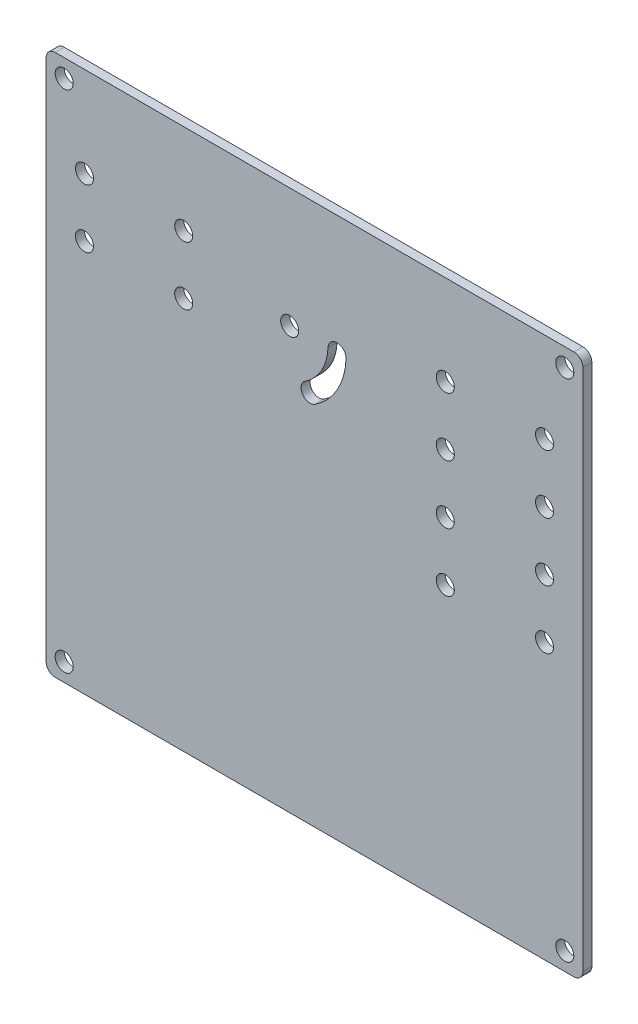
SolidWorks part; units mm, degrees
ref_plane "前视基准面" through (0, 0, 0) normal (0, 0, 1) x (1, 0, 0)
ref_plane "上视基准面" through (0, 0, 0) normal (0, 1, 0) x (1, 0, 0)
ref_plane "右视基准面" through (0, 0, 0) normal (1, 0, 0) x (0, 0, -1)
other "Configuration Table"
sketch "草图2" plane through (0, 0, 0) normal (0, 0, 1) x (1, 0, 0)
  line L1 (0, 0) -> (119, 0)
  line L2 (0, 0) -> (0, 120)
  line L3 (0, 120) -> (119, 120)
  line L4 (119, 0) -> (119, 120)
  dimension "D1" = 119
  dimension "D2" = 120
extrude "凸台-拉伸1" add sketch "草图2" along normal blind 2 contours L3 L4 L1 L2
sketch "草图4" plane through (0, 0, 2) normal (0, 0, 1) x (1, 0, 0)
  line L0 (0, 0) -> (0, 120) construction
  line L1 (8.5, 100) -> (30.5, 100) construction
  line L2 (8.5, 100) -> (8.5, 87) construction
  line L3 (8.5, 87) -> (30.5, 87) construction
  line L4 (30.5, 100) -> (30.5, 87) construction
  line L5 (119, 0) -> (119, 120) construction
  line L6 (54, 76.8623) -> (64.5, 76.8623) construction
  line L7 (54, 76.8623) -> (54, 93.5) construction
  line L8 (54, 93.5) -> (64.5, 93.5) construction
  line L9 (64.5, 76.8623) -> (64.5, 93.5) construction
  line L10 (88.5, 100) -> (110.5, 100) construction
  line L11 (88.5, 100) -> (88.5, 87) construction
  line L12 (88.5, 87) -> (110.5, 87) construction
  line L13 (110.5, 100) -> (110.5, 87) construction
  line L14 (88.5, 74) -> (110.5, 74) construction
  line L15 (88.5, 74) -> (88.5, 61) construction
  line L16 (88.5, 61) -> (110.5, 61) construction
  line L17 (110.5, 74) -> (110.5, 61) construction
  line L18 (0, 120) -> (119, 120) construction
  dimension "D1" = 8.5
  dimension "D2" = 22
  dimension "D3" = 13
  dimension "D4" = 23.5
  dimension "D5" = 10.5
  dimension "D6" = 8.5
  dimension "D7" = 22
  dimension "D8" = 13
  dimension "D9" = 22
  dimension "D10" = 13
  dimension "D11" = 8.5
  dimension "D12" = 6.5
  dimension "D13" = 20
  dimension "D14" = 0
  dimension "D15" = 13
sketch "草图6" plane through (0, 0, 0) normal (0, 0, 1) x (1, 0, 0)
  circle A0 centre (8.5, 100) radius 2
  circle A1 centre (30.5, 100) radius 2
  circle A2 centre (8.5, 87) radius 2
  circle A3 centre (30.5, 87) radius 2
  circle A4 centre (54, 93.5) radius 2
  circle A5 centre (88.5, 100) radius 2
  circle A6 centre (88.5, 87) radius 2
  circle A7 centre (110.5, 100) radius 2
  circle A8 centre (110.5, 87) radius 2
  circle A9 centre (88.5, 74) radius 2
  circle A10 centre (88.5, 61) radius 2
  circle A11 centre (110.5, 74) radius 2
  circle A12 centre (110.5, 61) radius 2
  point P5 (30.5, 100)
  point P9 (8.5, 87)
  point P13 (30.5, 87)
  point P17 (54, 93.5)
  point P21 (88.5, 100)
  point P25 (87.2251, 87)
  point P26 (88.5, 87)
  point P30 (110.5, 100)
  point P34 (110.5, 87)
  point P38 (88.5, 74)
  point P42 (88.5, 61)
  point P46 (111.5876, 74)
  point P47 (110.5, 74)
  point P51 (110.5, 61)
  point P55 (64.5, 93.5)
  dimension "D1" = 4
extrude "切除-拉伸3" cut sketch "草图6" along normal blind 2
sketch "草图7" plane through (0, 0, 0) normal (0, 0, 1) x (1, 0, 0)
  arc A1 (64.5, 93.5) -> (58.5211, 82.9054) centre (51.2464, 93.9951) cw construction
  arc A2 (59.6181, 81.2331) -> (66.4986, 93.4253) centre (51.2464, 93.9951) ccw
  arc A3 (57.4241, 84.5777) -> (62.5014, 93.5747) centre (51.2464, 93.9951) ccw
  arc A4 (57.4241, 84.5777) -> (59.6181, 81.2331) centre (58.5211, 82.9054) ccw
  arc A6 (62.5014, 93.5747) -> (66.4986, 93.4253) centre (64.5, 93.5) cw
  point P5 (62.7969, 87.4768)
  dimension "D2" = 15.2628
extrude "切除-拉伸5" cut sketch "草图7" along normal blind 2
fillet "圆角1" radius 2 4 edges at (119, 120, 1) (119, 0, 1) (0, 0, 1) (0, 120, 1)
sketch "草图9" plane through (0, 0, 2) normal (0, 0, 1) x (1, 0, 0)
  line L0 (2, 120) -> (117, 120) construction
  line L1 (4, 116) -> (115, 116) construction
  line L2 (4, 116) -> (4, 4) construction
  line L3 (4, 4) -> (115, 4) construction
  line L4 (115, 116) -> (115, 4) construction
  line L5 (0, 2) -> (0, 118) construction
  line L7 (119, 2) -> (119, 118) construction
  line L8 (2, 0) -> (117, 0) construction
  circle A0 centre (4, 116) radius 2
  circle A1 centre (115, 116) radius 2
  circle A2 centre (4, 4) radius 2
  circle A3 centre (115, 4) radius 2
  dimension "D5" = 4
  dimension "D6" = 4
  dimension "D7" = 4
  dimension "D8" = 4
  dimension "D1" = 4
  dimension "D2" = 4
  dimension "D3" = 4
  dimension "D4" = 4
extrude "切除-拉伸6" cut sketch "草图9" against normal blind 2
